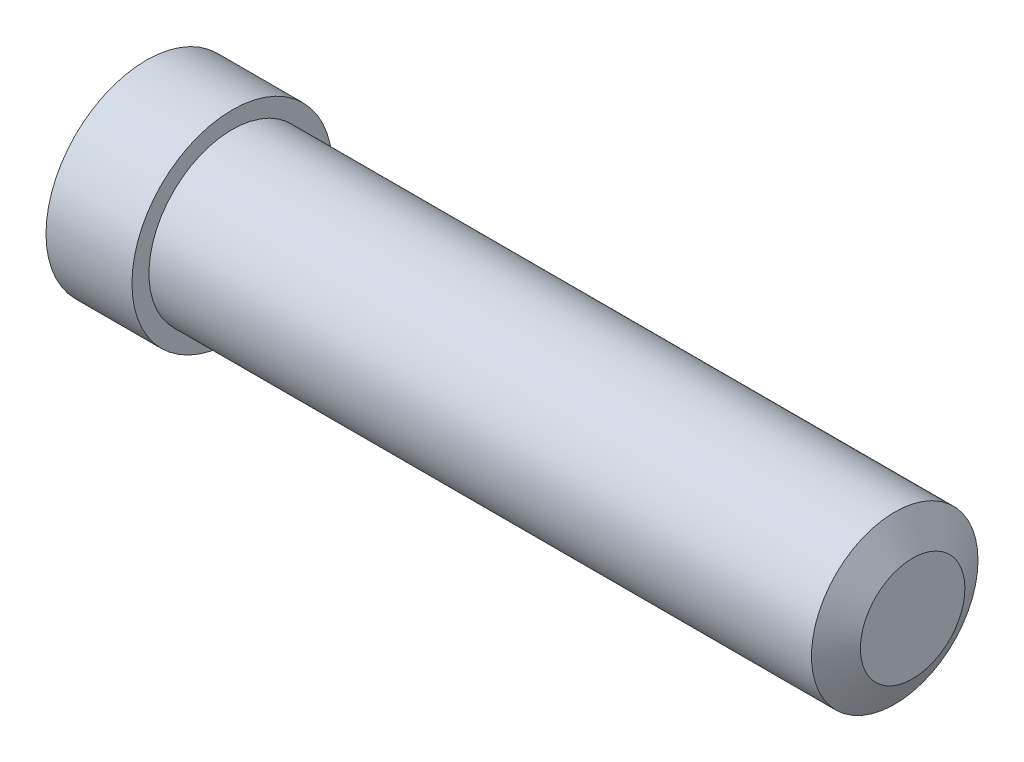
SolidWorks part; units mm, degrees
ref_plane "Front Plane" through (0, 0, 0) normal (0, 0, 1) x (1, 0, 0)
ref_plane "Top Plane" through (0, 0, 0) normal (0, 1, 0) x (1, 0, 0)
ref_plane "Right Plane" through (0, 0, 0) normal (1, 0, 0) x (0, 0, -1)
sketch "Sketch1" plane through (0, 0, 0) normal (1, 0, 0) x (0, 0, -1)
  circle A0 centre (0, 0) radius 1.4224
  dimension "D1" = 2.8448
extrude "Boss-Extrude1" add sketch "Sketch1" along normal blind 1.2192
sketch "Sketch2" plane through (1.2192, 0, 0) normal (1, 0, 0) x (0, 0, -1)
  circle A0 centre (0, 0) radius 1.1811
  dimension "D1" = 2.3622
extrude "Boss-Extrude2" add sketch "Sketch2" along normal blind 9.652
chamfer "Chamfer1" distance 0.254 angle 60 1 edges at (10.8712, 0, -1.1811)
